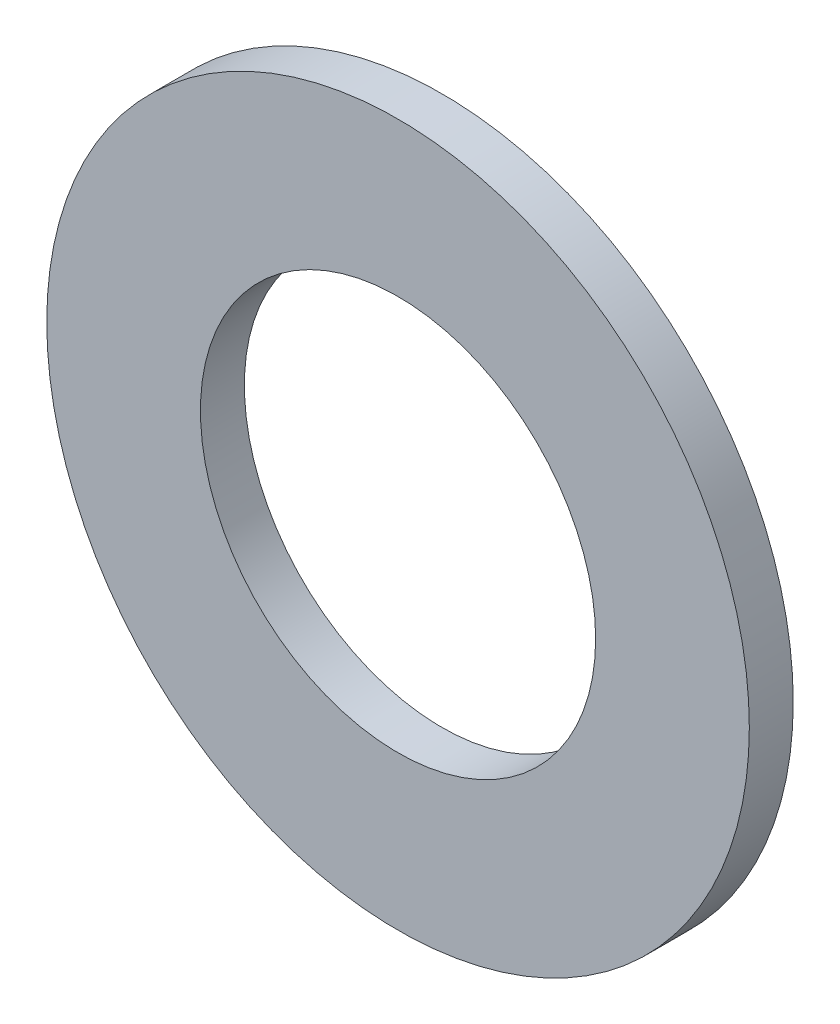
SolidWorks part; units mm, degrees
ref_plane "前视基准面" through (0, 0, 0) normal (0, 0, 1) x (1, 0, 0)
ref_plane "上视基准面" through (0, 0, 0) normal (0, 1, 0) x (1, 0, 0)
ref_plane "右视基准面" through (0, 0, 0) normal (1, 0, 0) x (0, 0, -1)
sketch "草图1" plane through (0, 0, 0) normal (0, 0, 1) x (1, 0, 0)
  circle A0 centre (0, 0) radius 8
  dimension "D1" = 16
extrude "凸台-拉伸1" add sketch "草图1" along normal blind 1
sketch "草图2" plane through (0, 0, 1) normal (0, 0, 1) x (1, 0, 0)
  circle A0 centre (0, 0) radius 4.5
  dimension "D1" = 9
extrude "切除-拉伸1" cut sketch "草图2" against normal through all
